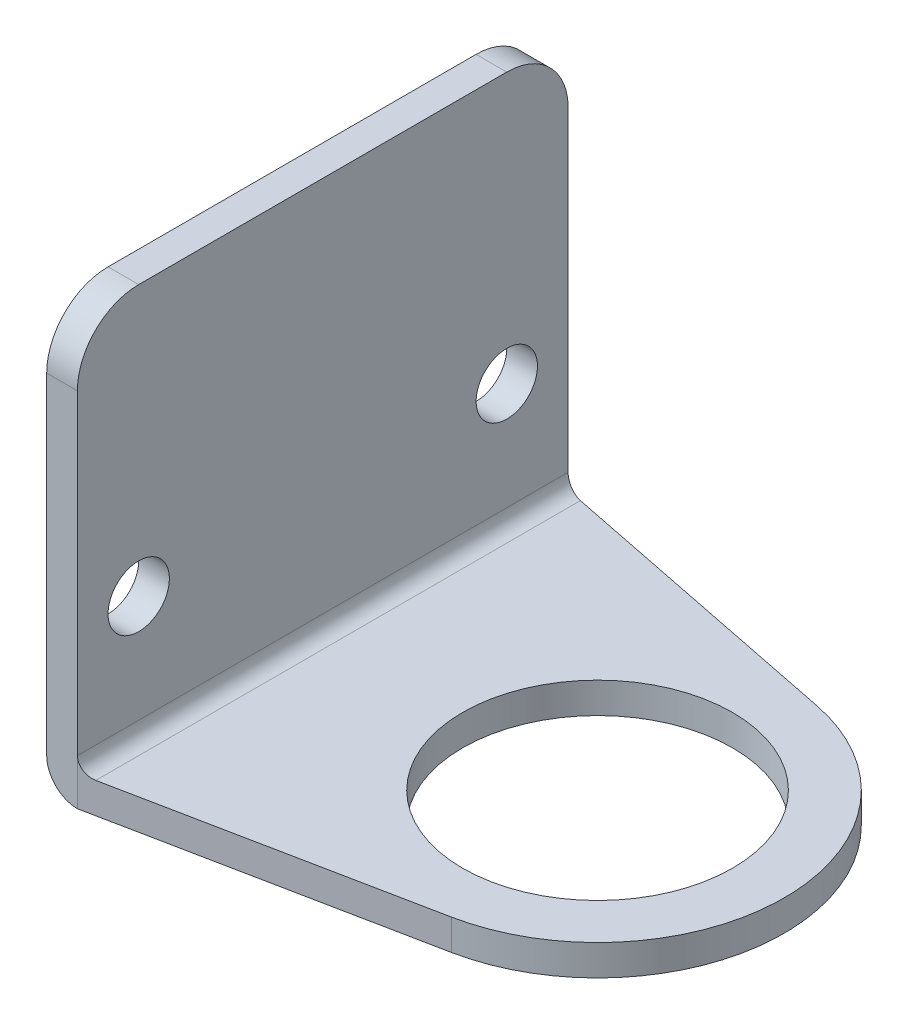
SolidWorks part; units mm, degrees
material "6061-T6 (SS)"
ref_plane "Front Plane" through (0, 0, 0) normal (0, 0, 1) x (1, 0, 0)
ref_plane "Top Plane" through (0, 0, 0) normal (0, 1, 0) x (1, 0, 0)
ref_plane "Right Plane" through (0, 0, 0) normal (1, 0, 0) x (0, 0, -1)
sketch "Sketch1" plane through (0, 0, 0) normal (0, 1, 0) x (1, 0, 0)
  line L0 (0, 0) -> (-28.448, 0)
  line L1 (-28.448, 0) -> (-28.448, 13.97)
  line L2 (-28.448, 13.97) -> (-28.448, -13.97)
  line L3 (-28.448, 13.97) -> (-28.448, 25.4)
  line L4 (-28.448, -13.97) -> (-28.448, -25.4)
  line L5 (-28.448, -25.4) -> (3.7994, -18.9264)
  line L6 (-28.448, 25.4) -> (3.7994, 18.9264)
  line L8 (-28.448, 25.4) -> (-31.623, 25.4)
  line L9 (-28.448, 25.4) -> (-28.448, -25.4)
  line L10 (-28.448, -25.4) -> (-31.623, -25.4)
  line L11 (-31.623, 25.4) -> (-31.623, -25.4)
  circle A0 centre (0, 0) radius 13.97
  circle A1 centre (0, 0) radius 19.304
  dimension "D1" = 38.608
  dimension "D8" = 27.94
  dimension "D2" = 28.448
  dimension "D3" = 13.97
  dimension "D4" = 27.94
  dimension "D5" = 11.43
  dimension "D6" = 11.43
  dimension "D7" = 3.175
extrude "Boss-Extrude1" add sketch "Sketch1" along normal blind 3.175
sketch "Sketch2" plane through (0, 3.175, 0) normal (0, 1, 0) x (1, 0, 0)
  line L0 (-28.448, -25.4) -> (-31.623, -25.4) construction
  line L1 (-28.448, 25.4) -> (-31.623, 25.4) construction
  line L2 (-31.623, 25.4) -> (-31.623, -25.4) construction
  line L3 (-28.448, -25.4) -> (-31.623, -25.4)
  line L4 (-28.448, 25.4) -> (-31.623, 25.4)
  line L5 (-31.623, 25.4) -> (-31.623, -25.4)
  line L7 (-28.448, 25.4) -> (-31.623, 25.4)
  line L8 (-28.448, 25.4) -> (-28.448, -25.4)
  line L9 (-28.448, -25.4) -> (-31.623, -25.4)
  line L10 (-31.623, 25.4) -> (-31.623, -25.4)
  line M4 (-28.448, 25.4) -> (-31.623, 25.4)
  line M5 (-31.623, 25.4) -> (-31.623, -25.4)
  line M6 (-31.623, -25.4) -> (-28.448, -25.4)
extrude "Boss-Extrude2" add sketch "Sketch2" along normal blind 40.64 contours L8 M4 M5 M6
sketch "Sketch6" plane through (-31.623, 0, 0) normal (-1, 0, 0) x (0, 0, 1)
  line L0 (0, 43.815) -> (-13.97, 43.815)
  line L1 (-25.4, 43.815) -> (25.4, 43.815) construction
  line L2 (-25.4, 0) -> (25.4, 0) construction
  line L3 (-13.97, 43.815) -> (13.97, 43.815)
  line L4 (-13.97, 43.815) -> (-13.97, 0)
  line L5 (-13.97, 0) -> (13.97, 0)
  line L6 (13.97, 43.815) -> (13.97, 0)
  line L7 (25.4, 43.815) -> (25.4, 3.175) construction
  line L8 (-25.4, 0) -> (-13.97, 0)
  line L9 (-13.97, 0) -> (-19.685, 0)
  line L10 (-19.685, 0) -> (-19.685, 43.815)
  line L11 (-19.685, 43.815) -> (-19.685, 21.9075)
  line L12 (-19.685, 21.9075) -> (25.4, 21.9075)
  line L13 (25.4, 43.815) -> (25.4, 0) construction
  line L14 (25.4, 21.9075) -> (13.97, 21.9075)
  line L15 (13.97, 21.9075) -> (19.685, 21.9075)
  line L16 (-25.4, 43.815) -> (-25.4, 3.175) construction
  line L17 (25.4, 3.175) -> (18.9264, 3.175) construction
  line L18 (18.9264, 3.175) -> (-18.9264, 3.175) construction
  circle A0 centre (-19.05, 15.875) radius 3.175
  circle A1 centre (19.05, 15.875) radius 3.175
  dimension "D1" = 6.35
  dimension "D4" = 6.35
  dimension "D2" = 13.97
  dimension "D3" = 27.94
  dimension "D5" = 6.35
  dimension "D6" = 6.35
  dimension "D7" = 12.7
  dimension "D8" = 12.7
fillet "Fillet1" radius 1.5875 1 edges at (-28.448, 3.175, 0)
fillet "Fillet2" radius 3.175 1 edges at (-31.623, 0, 0)
extrude "Cut-Extrude2" cut sketch "Sketch6" against normal through all contours A1 | A0
fillet "Fillet3" radius 6.35 2 edges at (-30.0355, 43.815, -25.4) (-30.0355, 43.815, 25.4)
